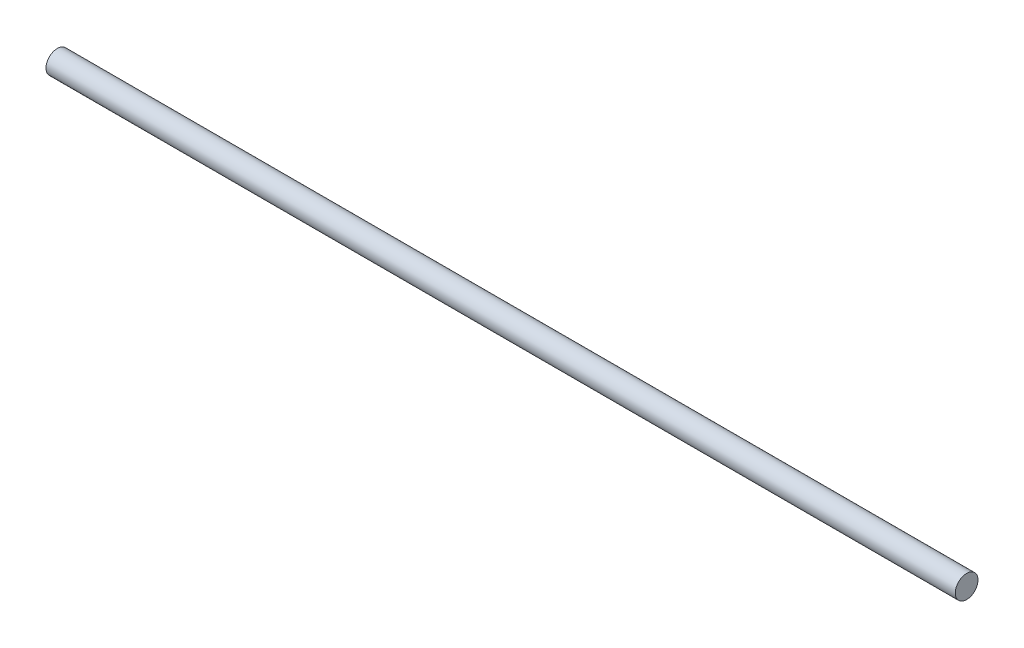
SolidWorks part; units mm, degrees
ref_plane "Front Plane" through (0, 0, 0) normal (0, 0, 1) x (1, 0, 0)
ref_plane "Top Plane" through (0, 0, 0) normal (0, 1, 0) x (1, 0, 0)
ref_plane "Right Plane" through (0, 0, 0) normal (1, 0, 0) x (0, 0, -1)
sketch "Sketch1" plane through (0, 0, 0) normal (1, 0, 0) x (0, 0, -1)
  circle A0 centre (0, 0) radius 2.5
  dimension "D1" = 5
extrude "Boss-Extrude1" add sketch "Sketch1" along normal mid plane 200
